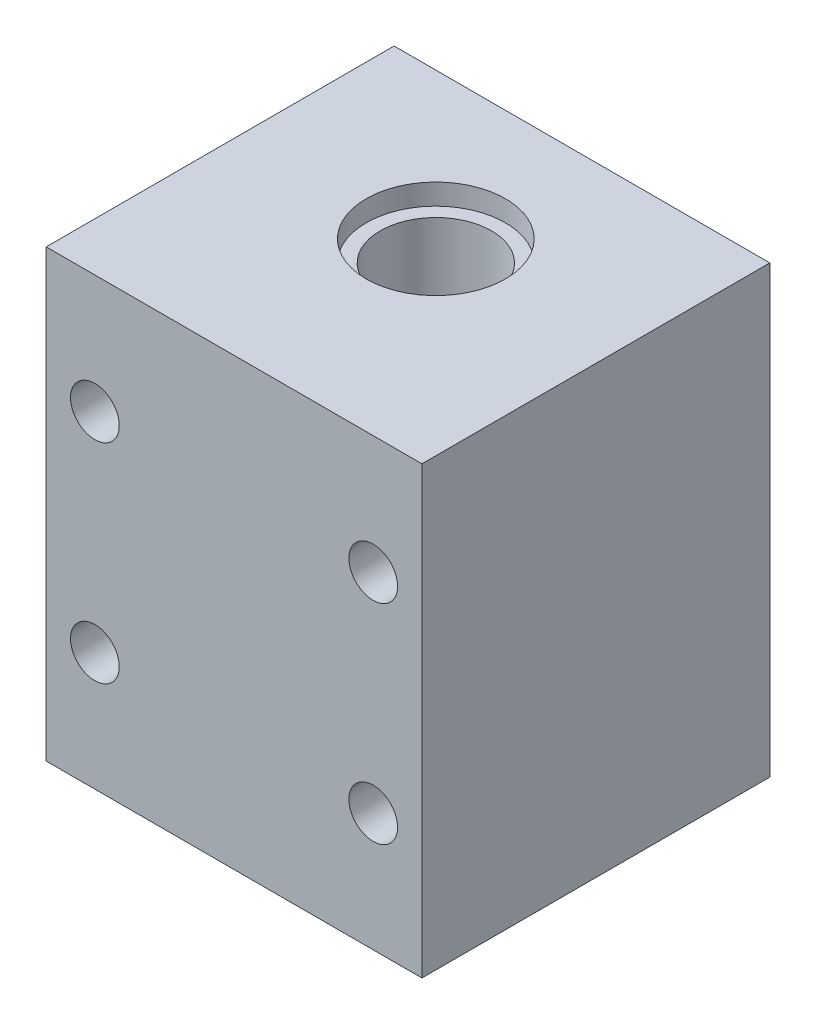
SolidWorks part; units mm, degrees
other "Annotazione1"
sketch "Schizzo6" plane through (-13.5, 16, 31) normal (-0.0709, 0.1103, 0.9914) x (0.8585, -0.4994, 0.1169)
ref_plane "Piano frontale" through (0, 0, 0) normal (0, 0, 1) x (1, 0, 0)
ref_plane "Piano superiore" through (0, 0, 0) normal (0, 1, 0) x (1, 0, 0)
ref_plane "Piano destro" through (0, 0, 0) normal (1, 0, 0) x (0, 0, -1)
sketch "Schizzo1" plane through (0, 0, 0) normal (0, 0, 1) x (1, 0, 0)
  line L1 (-13.5, 16) -> (13.5, 16)
  line L2 (-13.5, 16) -> (-13.5, -16)
  line L3 (-13.5, -16) -> (13.5, -16)
  line L4 (13.5, 16) -> (13.5, -16)
  line L5 (-13.5, 16) -> (13.5, -16) construction
  line L6 (-13.5, -16) -> (13.5, 16) construction
  point P0 (0, 0)
  dimension "D1" = 27
  dimension "D2" = 32
extrude "Estrusione-Estrusione1" add sketch "Schizzo1" along normal blind 31
sketch "Schizzo2" plane through (0, 0, 0) normal (0, 0, -1) x (-1, 0, 0)
  line L1 (-10, 7.5) -> (10, 7.5) construction
  line L2 (-10, 7.5) -> (-10, -7.5) construction
  line L3 (-10, -7.5) -> (10, -7.5) construction
  line L4 (10, 7.5) -> (10, -7.5) construction
  line L5 (-10, 7.5) -> (10, -7.5) construction
  line L6 (-10, -7.5) -> (10, 7.5) construction
  circle A0 centre (-10, 7.5) radius 1.75
  circle A1 centre (10, 7.5) radius 1.75
  circle A2 centre (10, -7.5) radius 1.75
  circle A3 centre (-10, -7.5) radius 1.75
  point P0 (0, 0)
  dimension "D3" = 3.5
  dimension "D1" = 20
  dimension "D2" = 15
extrude "Taglio-Estrusione1" cut sketch "Schizzo2" against normal through all
sketch "Schizzo8" plane through (0, 16, 0) normal (0, 1, 0) x (1, 0, 0)
  line L0 (13.5, -31) -> (13.5, 0) construction
  line L1 (-13.5, -31) -> (13.5, -31)
  line L2 (-13.5, -31) -> (-13.5, -6)
  line L3 (-13.5, -6) -> (13.5, -6)
  line L4 (13.5, -31) -> (13.5, -6)
  dimension "D1" = 25
extrude "Taglio-Estrusione7" cut sketch "Schizzo8" against normal through all flip side to cut
sketch "Schizzo10" plane through (0, 16, 0) normal (0, 1, 0) x (1, 0, 0)
  line L0 (0, -31) -> (0, -6) construction
  line L1 (13.5, -31) -> (-13.5, -31) construction
  line L2 (13.5, -6) -> (-13.5, -6) construction
  circle A0 centre (0, -16.5) radius 5
  dimension "D1" = 10
  dimension "D2" = 14.5
extrude "Taglio-Estrusione8" cut sketch "Schizzo10" against normal blind 1.5
sketch "Schizzo11" plane through (0, 16, 0) normal (0, 1, 0) x (1, 0, 0)
  circle A0 centre (0, -16.5) radius 4
  dimension "D1" = 8
extrude "Taglio-Estrusione9" cut sketch "Schizzo11" against normal through all
sketch "Schizzo12" plane through (0, -16, 0) normal (0, -1, 0) x (1, 0, 0)
  circle A0 centre (0, 16.5) radius 5
  dimension "D1" = 10
extrude "Taglio-Estrusione10" cut sketch "Schizzo12" against normal blind 1.5
